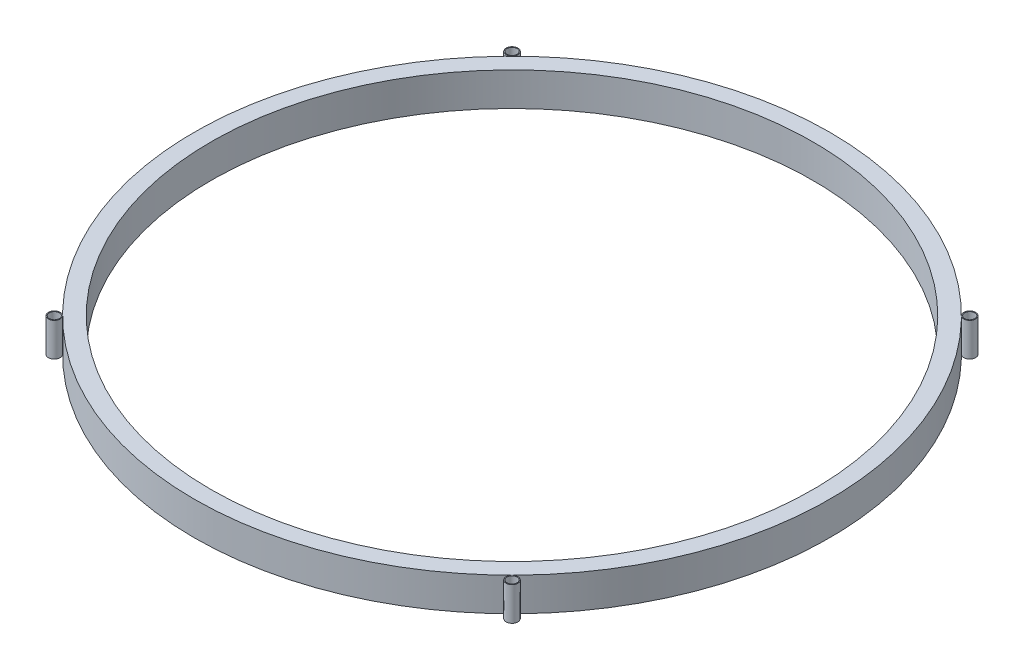
SolidWorks part; units mm, degrees
ref_plane "Спереди" through (0, 0, 0) normal (0, 0, 1) x (1, 0, 0)
ref_plane "Сверху" through (0, 0, 0) normal (0, 1, 0) x (1, 0, 0)
ref_plane "Справа" through (0, 0, 0) normal (1, 0, 0) x (0, 0, -1)
sketch "Эскиз1" plane through (0, 0, 0) normal (0, 1, 0) x (1, 0, 0)
  line L0 (-67.1751, 67.1751) -> (67.1751, -67.1751) construction
  line L1 (0, 95) -> (0, -95) construction
  line L2 (67.1751, 67.1751) -> (-67.1751, -67.1751) construction
  line L3 (67.1751, 67.1751) -> (69.65, 69.65) construction
  circle A0 centre (0, 0) radius 95
  circle A1 centre (0, 0) radius 90
  circle A2 centre (68.4126, 68.4126) radius 1.75
  circle A3 centre (68.4126, 68.4126) radius 1.5
  circle A4 centre (68.4126, -68.4126) radius 1.75
  circle A5 centre (68.4126, -68.4126) radius 1.5
  circle A6 centre (-68.4126, -68.4126) radius 1.75
  circle A7 centre (-68.4126, -68.4126) radius 1.5
  circle A8 centre (-68.4126, 68.4126) radius 1.75
  circle A9 centre (-68.4126, 68.4126) radius 1.5
  circle A10 centre (0, 0) radius 96.75 construction
  point P26 (0, 0)
  dimension "D1" = 180
  dimension "D2" = 190
  dimension "D4" = 3.5
  dimension "D5" = 3
  dimension "D3" = 45
  dimension "D6" = 4
extrude "Бобышка-Вытянуть2" add sketch "Эскиз1" along normal blind 10 contours A0 A1 | A3 | A2 | A5 | A4 | A7 | A6 | A9 | A8
sketch "Эскиз2" plane through (0, 10, 0) normal (0, 1, 0) x (1, 0, 0)
  line L0 (-68.4126, -66.9126) -> (-68.4126, -69.9126) construction
  line L1 (-69.9126, -68.4126) -> (-66.9126, -68.4126) construction
  line L2 (-68.4126, 69.9126) -> (-68.4126, 66.9126) construction
  line L3 (-69.9126, 68.4126) -> (-66.9126, 68.4126) construction
  circle A0 centre (-68.4126, -68.4126) radius 1.5 construction
  circle A1 centre (-68.4126, 68.4126) radius 1.5 construction
  point P14 (-68.4126, 68.4126)
  point P15 (-68.4126, -68.4126)
  point P16 (68.4126, -68.4126)
  point P17 (68.4126, 68.4126)
